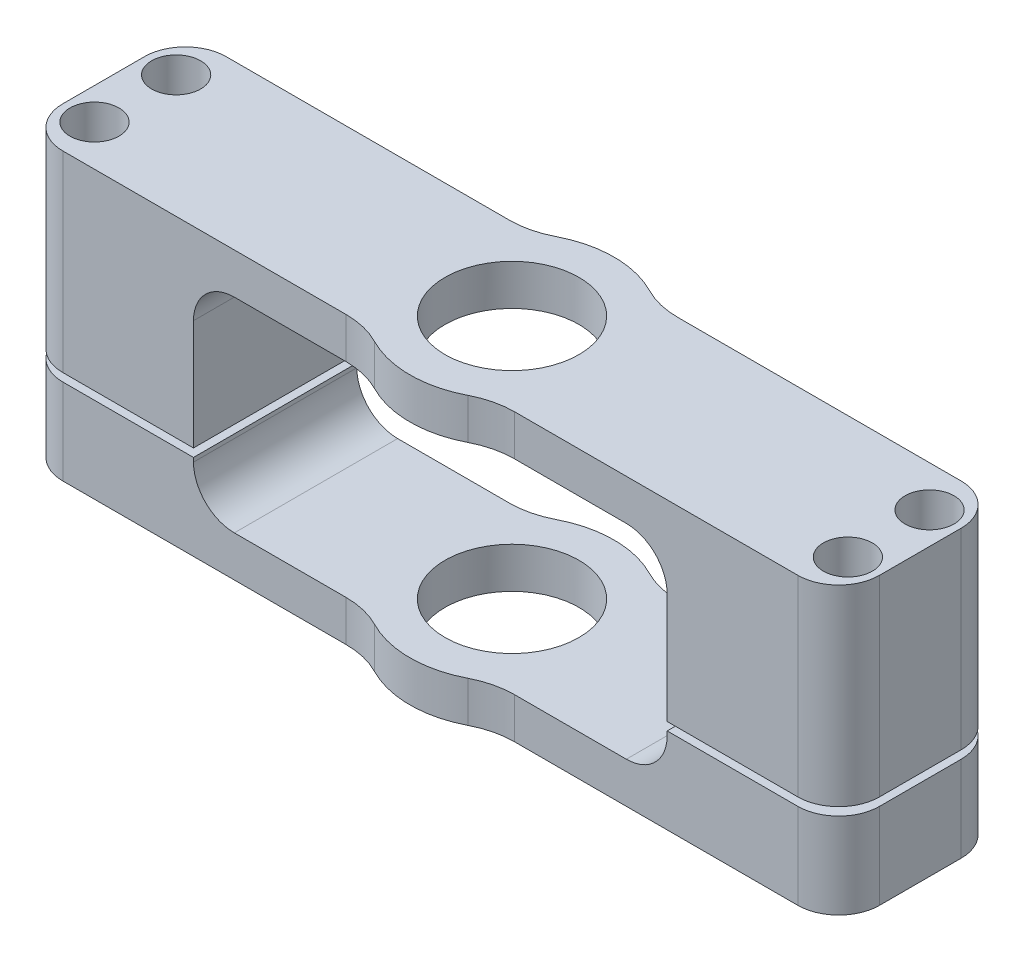
SolidWorks part; units mm, degrees
ref_plane "Front Plane" through (0, 0, 0) normal (0, 0, 1) x (1, 0, 0)
ref_plane "Top Plane" through (0, 0, 0) normal (0, 1, 0) x (1, 0, 0)
ref_plane "Right Plane" through (0, 0, 0) normal (1, 0, 0) x (0, 0, -1)
sketch "Sketch1" plane through (0, 0, 0) normal (0, 1, 0) x (1, 0, 0)
  line L0 (-44, 0) -> (-44, -44) construction
  line L1 (-44, -44) -> (44, -44) construction
  line L2 (44, -44) -> (44, 0) construction
  line L4 (-44, -10) -> (44, -10)
  line L5 (-44, -10) -> (-44, 10)
  line L6 (-44, 10) -> (44, 10)
  line L7 (44, -10) -> (44, 10)
  line L8 (-44, -10) -> (44, 10) construction
  line L9 (-44, 10) -> (44, -10) construction
  arc A0 (44, 0) -> (-44, 0) centre (0, 0) ccw construction
  dimension "D1" = 88
  dimension "D2" = 88
  dimension "D3" = 20
extrude "Boss-Extrude1" add sketch "Sketch1" along normal blind 35
sketch "Sketch2" plane through (0, 0, 10) normal (0, 0, 1) x (1, 0, 0)
  line L0 (-44, 0) -> (44, 0) construction
  line L1 (-1044, 11) -> (48956, 11) construction
  line L2 (0, -1000) -> (0, 49000) construction
  line L3 (-44, 35) -> (-44, 0) construction
  circle A0 centre (-38, 11) radius 4.25
  circle A1 centre (38, 11) radius 4.25
  point P2 (-44, 17.5)
  dimension "D1" = 8.5
  dimension "D2" = 6
  dimension "D3" = 11
extrude "Cut-Extrude1" cut sketch "Sketch2" against normal through all
sketch "Sketch7" plane through (0, 35, 0) normal (0, 1, 0) x (1, 0, 0)
  circle A0 centre (0, 0) radius 12.5
  dimension "D1" = 25
extrude "Boss-Extrude2" add sketch "Sketch7" against normal up to surface (35 mm away) up to face at (0, 0, 0)
sketch "Sketch4" plane through (0, 35, 0) normal (0, 1, 0) x (1, 0, 0)
  circle A0 centre (0, 0) radius 8.2
  dimension "D1" = 16.4
extrude "Cut-Extrude3" cut sketch "Sketch4" against normal through all
fillet "Fillet2" radius 10 4 edges at (-7.5, 17.5, 10) (7.5, 17.5, 10) (7.5, 17.5, -10) (-7.5, 17.5, -10)
sketch "Sketch10" plane through (0, 0, 0) normal (0, 0, 1) x (1, 0, 0)
  line L0 (44, 0) -> (10.3078, 0) construction
  line L1 (29, 30) -> (-29, 30)
  line L2 (29, 30) -> (29, 5)
  line L3 (29, 5) -> (-29, 5)
  line L4 (-29, 30) -> (-29, 5)
  line L6 (-44, 35) -> (-44, 0) construction
  line L7 (44, 35) -> (44, 0) construction
  line L8 (44, 35) -> (10.3078, 35) construction
  dimension "D1" = 5
  dimension "D2" = 15
  dimension "D3" = 15
  dimension "D4" = 5
extrude "Cut-Extrude5" cut sketch "Sketch10" against normal through all and the other way through all
fillet "Fillet3" radius 5 4 edges at (-29, 5, 0) (29, 5, 0) (-29, 30, 0) (29, 30, 0)
sketch "Sketch11" plane through (44, 0, 0) normal (1, 0, 0) x (0, 0, -1)
  line L4 (10, 0) -> (10, 35)
  line L5 (10, 35) -> (-10, 35)
  line L6 (-10, 35) -> (-10, 0)
  line L7 (-10, 0) -> (10, 0)
  line L8 (10, 0) -> (10, 35)
  line L10 (-10, 35) -> (-10, 0)
  line L11 (-10, 0) -> (10, 0)
  line L13 (10, 35) -> (-10, 35)
  dimension "D1" = 0
extrude "Boss-Extrude3" add sketch "Sketch11" along normal blind 6
sketch "Sketch12" plane through (0, 35, 0) normal (0, 1, 0) x (1, 0, 0)
  line L2 (50, 10) -> (10.3078, 10) construction
  line L3 (10.3078, -10) -> (50, -10) construction
  circle A0 centre (46.1249, 5) radius 1.6
  circle A1 centre (46.1249, -5) radius 1.6
  dimension "D1" = 3.2
  dimension "D2" = 5
  dimension "D3" = 5
extrude "Cut-Extrude6" cut sketch "Sketch12" against normal through all
mirror "Mirror1" about plane through (0, 0, 0) normal (1, 0, 0) of "Cut-Extrude6", "Boss-Extrude3"
fillet "Fillet5" radius 5 4 edges at (50, 17.5, -10) (50, 17.5, 10) (-50, 17.5, 10) (-50, 17.5, -10)
sketch "Sketch13" plane through (0, 0, 10) normal (0, 0, 1) x (1, 0, 0)
  circle A4 centre (38, 11) radius 4.25 construction
  circle A5 centre (38, 11) radius 4.25
  circle A6 centre (-38, 11) radius 4.25 construction
  circle A7 centre (-38, 11) radius 4.25
extrude "Boss-Extrude4" add sketch "Sketch13" against normal blind 4
sketch "Sketch14" plane through (0, 0, -10) normal (0, 0, -1) x (-1, 0, 0)
  line L1 (-50, 10.5) -> (50, 10.5)
  line L2 (-50, 10.5) -> (-50, 11.5)
  line L3 (-50, 11.5) -> (50, 11.5)
  line L4 (50, 10.5) -> (50, 11.5)
  line L5 (-50, 10.5) -> (50, 11.5) construction
  line L6 (-50, 11.5) -> (50, 10.5) construction
  line L7 (50, 35) -> (50, 0) construction
  point P0 (0, 11)
  point P8 (38, 11)
  dimension "D1" = 1
extrude "Cut-Extrude7" cut sketch "Sketch14" against normal through all
sketch "Sketch15" plane through (0, 35, 0) normal (0, 1, 0) x (1, 0, 0)
  circle A0 centre (-46.1249, 5) radius 3
  circle A1 centre (-46.1249, -5) radius 3
  circle A2 centre (46.1249, 5) radius 3
  circle A3 centre (46.1249, -5) radius 3
  dimension "D1" = 6
extrude "Cut-Extrude8" cut sketch "Sketch15" against normal blind 6
sketch "Sketch16" plane through (0, 0, 0) normal (0, -1, 0) x (1, 0, 0)
  line L1 (-42.9494, 5) -> (-44.5371, 7.75)
  line L2 (-44.5371, 7.75) -> (-47.7126, 7.75)
  line L3 (-47.7126, 7.75) -> (-49.3003, 5)
  line L4 (-49.3003, 5) -> (-47.7126, 2.25)
  line L5 (-47.7126, 2.25) -> (-44.5371, 2.25)
  line L6 (-44.5371, 2.25) -> (-42.9494, 5)
  line L7 (-42.9494, -5) -> (-44.5371, -2.25)
  line L8 (-44.5371, -2.25) -> (-47.7126, -2.25)
  line L9 (-47.7126, -2.25) -> (-49.3003, -5)
  line L10 (-49.3003, -5) -> (-47.7126, -7.75)
  line L11 (-47.7126, -7.75) -> (-44.5371, -7.75)
  line L12 (-44.5371, -7.75) -> (-42.9494, -5)
  line L13 (49.3003, 5) -> (47.7126, 7.75)
  line L14 (47.7126, 7.75) -> (44.5371, 7.75)
  line L15 (44.5371, 7.75) -> (42.9494, 5)
  line L16 (42.9494, 5) -> (44.5371, 2.25)
  line L17 (44.5371, 2.25) -> (47.7126, 2.25)
  line L18 (47.7126, 2.25) -> (49.3003, 5)
  line L19 (49.3003, -5) -> (47.7126, -2.25)
  line L20 (47.7126, -2.25) -> (44.5371, -2.25)
  line L21 (44.5371, -2.25) -> (42.9494, -5)
  line L22 (42.9494, -5) -> (44.5371, -7.75)
  line L23 (44.5371, -7.75) -> (47.7126, -7.75)
  line L24 (47.7126, -7.75) -> (49.3003, -5)
  circle A0 centre (-46.1249, 5) radius 2.75 construction
  circle A1 centre (-46.1249, -5) radius 2.75 construction
  circle A2 centre (46.1249, 5) radius 2.75 construction
  circle A3 centre (46.1249, -5) radius 2.75 construction
  dimension "D1" = 5.5
extrude "Cut-Extrude9" cut sketch "Sketch16" against normal blind 3
